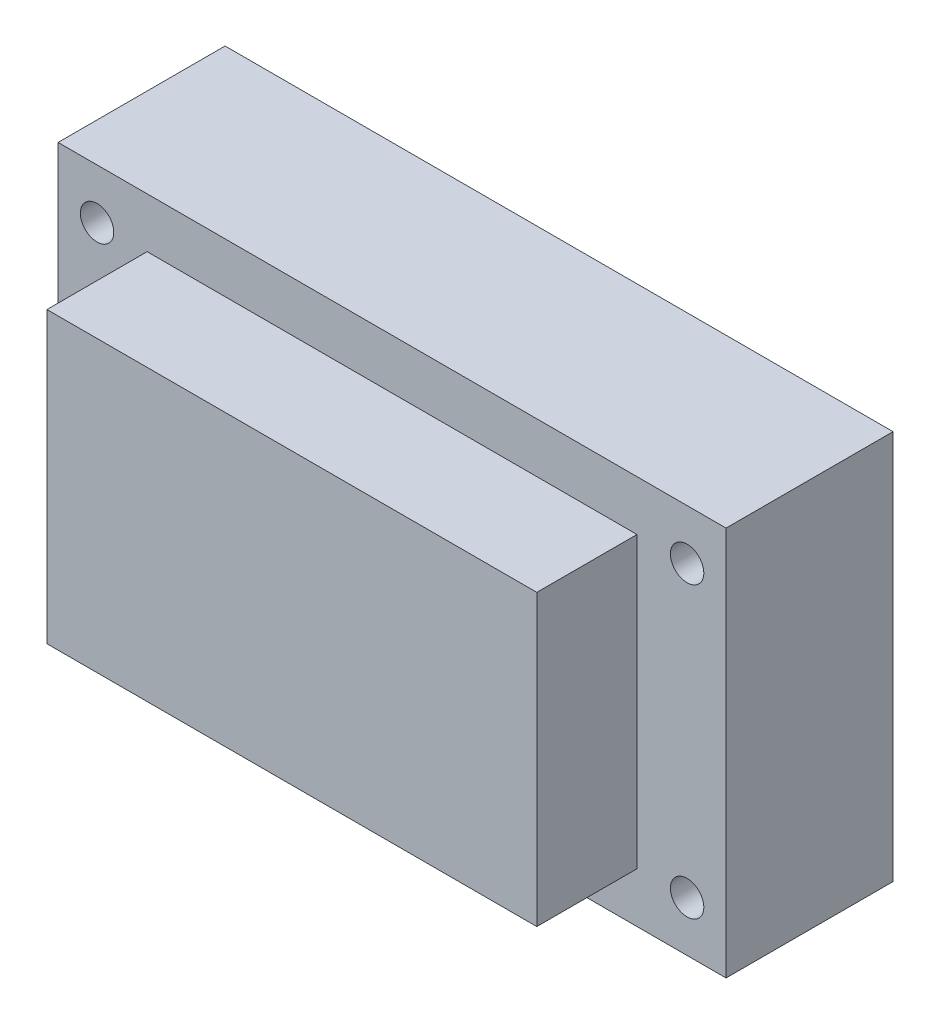
SolidWorks part; units mm, degrees
ref_plane "Alzado" through (0, 0, 0) normal (0, 0, 1) x (1, 0, 0)
ref_plane "Planta" through (0, 0, 0) normal (0, 1, 0) x (1, 0, 0)
ref_plane "Vista lateral" through (0, 0, 0) normal (1, 0, 0) x (0, 0, -1)
sketch "Croquis1" plane through (0, 0, 0) normal (0, 0, 1) x (1, 0, 0)
  line L1 (0, 0) -> (44, 0)
  line L2 (0, 0) -> (0, 26)
  line L3 (0, 26) -> (44, 26)
  line L4 (44, 0) -> (44, 26)
  dimension "D1" = 26
  dimension "D2" = 44
extrude "Saliente-Extruir1" add sketch "Croquis1" along normal blind 9
sketch "Croquis2" plane through (0, 0, 0) normal (0, 0, -1) x (-1, 0, 0)
  line L0 (-22, 26) -> (-22, 0) construction
  line L1 (-44, 26) -> (0, 26) construction
  line L2 (0, 0) -> (-44, 0) construction
  line L3 (-22, 0) -> (0, 13) construction
  line L4 (0, 26) -> (0, 0) construction
  line L5 (0, 13) -> (-44, 13) construction
  line L6 (-44, 0) -> (-44, 26) construction
  line L7 (-48.5, 26) -> (-48.5, 0) construction
  line L8 (-52, 30.5) -> (8, 30.5)
  line L9 (-52, 30.5) -> (-52, -4.5)
  line L10 (-52, -4.5) -> (8, -4.5)
  line L11 (8, 30.5) -> (8, -4.5)
  line L12 (-52, 30.5) -> (8, -4.5) construction
  line L13 (-52, -4.5) -> (8, 30.5) construction
  circle A0 centre (-48.5, 26) radius 1.5
  circle A1 centre (4.5, 26) radius 1.5
  circle A2 centre (-48.5, 0) radius 1.5
  circle A3 centre (4.5, 0) radius 1.5
  point P6 (-22, 13)
  dimension "D3" = 3
  dimension "D6" = 4.5
  dimension "D1" = 60
  dimension "D2" = 35
  dimension "D4" = 26.5
  dimension "D5" = 26
extrude "Saliente-Extruir2" add sketch "Croquis2" along normal blind 15
